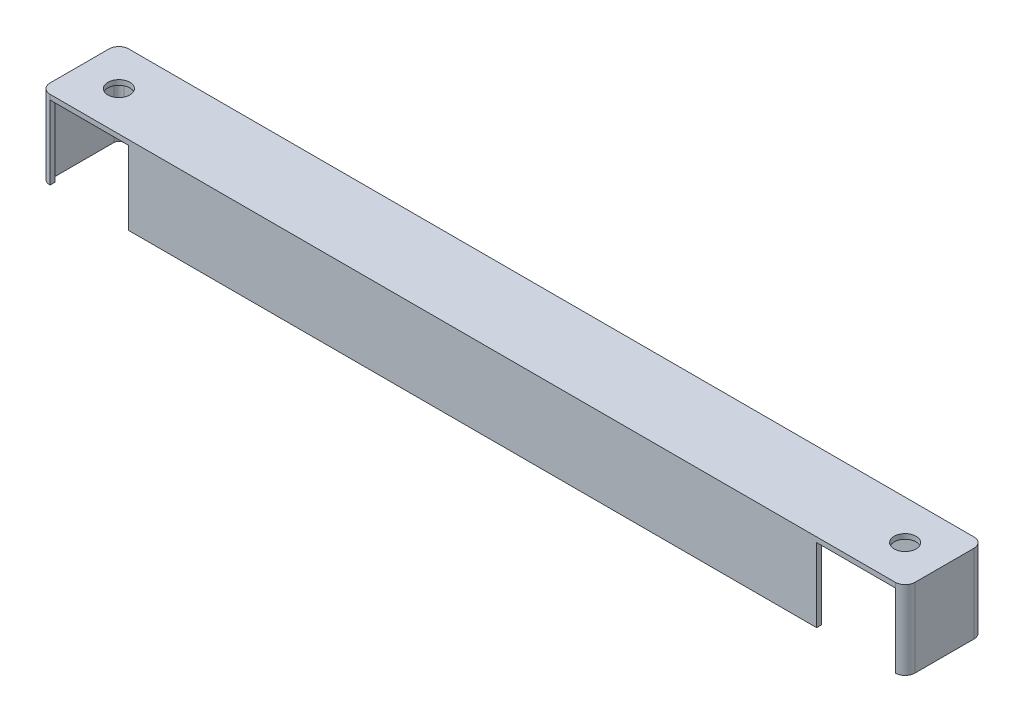
SolidWorks part; units mm, degrees
ref_plane "Front Plane" through (0, 0, 0) normal (0, 0, 1) x (1, 0, 0)
ref_plane "Top Plane" through (0, 0, 0) normal (0, 1, 0) x (1, 0, 0)
ref_plane "Right Plane" through (0, 0, 0) normal (1, 0, 0) x (0, 0, -1)
sketch "Sketch1" plane through (0, 0, 0) normal (0, 1, 0) x (1, 0, 0)
  line L1 (-136.525, -12.7) -> (136.525, -12.7)
  line L2 (-139.7, -9.525) -> (-139.7, 9.525)
  line L3 (-136.525, 12.7) -> (136.525, 12.7)
  line L4 (139.7, -9.525) -> (139.7, 9.525)
  line L5 (-139.7, -12.7) -> (139.7, 12.7) construction
  line L6 (-139.7, 12.7) -> (139.7, -12.7) construction
  line L8 (-139.7, 12.7) -> (-114.3, -12.7) construction
  line L9 (139.7, 12.7) -> (114.3, -12.7) construction
  circle A0 centre (127, 0) radius 3.556
  circle A1 centre (-127, 0) radius 3.556
  arc A2 (136.525, 12.7) -> (139.7, 9.525) centre (136.525, 9.525) cw
  arc A3 (136.525, -12.7) -> (139.7, -9.525) centre (136.525, -9.525) ccw
  arc A4 (-136.525, -12.7) -> (-139.7, -9.525) centre (-136.525, -9.525) cw
  arc A5 (-139.7, 9.525) -> (-136.525, 12.7) centre (-136.525, 9.525) cw
  point P0 (0, 0)
  dimension "D5" = 3.175
  dimension "D6" = 7.112
  dimension "D1" = 279.4
  dimension "D2" = 25.4
  dimension "D3" = 25.4
  dimension "D4" = 25.4
extrude "Boss-Extrude3" add sketch "Sketch1" along normal blind 25.4
sketch "Sketch5" plane through (0, 0, 0) normal (0, -1, 0) x (1, 0, 0)
  line L7 (-136.525, 11.1125) -> (-136.525, 12.7)
  line L8 (-136.525, 12.7) -> (-111.125, 12.7)
  line L9 (-136.525, 12.7) -> (136.525, 12.7) construction
  line L10 (-111.125, 12.7) -> (-111.125, 11.1125)
  line L11 (138.1125, -9.525) -> (138.1125, 9.525)
  line L12 (-136.525, -11.1125) -> (136.525, -11.1125)
  line L13 (-138.1125, 9.525) -> (-138.1125, -9.525)
  line L14 (136.525, 11.1125) -> (-136.525, 11.1125)
  line L15 (138.1125, -9.525) -> (138.1125, 9.525)
  line L16 (-136.525, -11.1125) -> (136.525, -11.1125)
  line L17 (-138.1125, 9.525) -> (-138.1125, -9.525)
  line L18 (111.125, 11.1125) -> (-111.125, 11.1125)
  line L19 (136.525, 11.1125) -> (136.525, 12.7)
  line L20 (136.525, 12.7) -> (111.125, 12.7)
  line L21 (111.125, 12.7) -> (111.125, 11.1125)
  arc A10 (138.1125, 9.525) -> (136.525, 11.1125) centre (136.525, 9.525) ccw
  arc A11 (138.1125, 9.525) -> (136.525, 11.1125) centre (136.525, 9.525) ccw
  arc A12 (136.525, -11.1125) -> (138.1125, -9.525) centre (136.525, -9.525) ccw
  arc A13 (136.525, -11.1125) -> (138.1125, -9.525) centre (136.525, -9.525) ccw
  arc A14 (-138.1125, -9.525) -> (-136.525, -11.1125) centre (-136.525, -9.525) ccw
  arc A15 (-138.1125, -9.525) -> (-136.525, -11.1125) centre (-136.525, -9.525) ccw
  arc A16 (-136.525, 11.1125) -> (-138.1125, 9.525) centre (-136.525, 9.525) ccw
  arc A17 (-136.525, 11.1125) -> (-138.1125, 9.525) centre (-136.525, 9.525) ccw
  point P9 (-136.525, 10.8198)
  point P10 (136.525, 10.7638)
  dimension "D2" = 25.4
  dimension "D3" = 25.4
  dimension "D1" = 1.5875
extrude "Cut-Extrude3" cut sketch "Sketch5" against normal blind 23.8125
